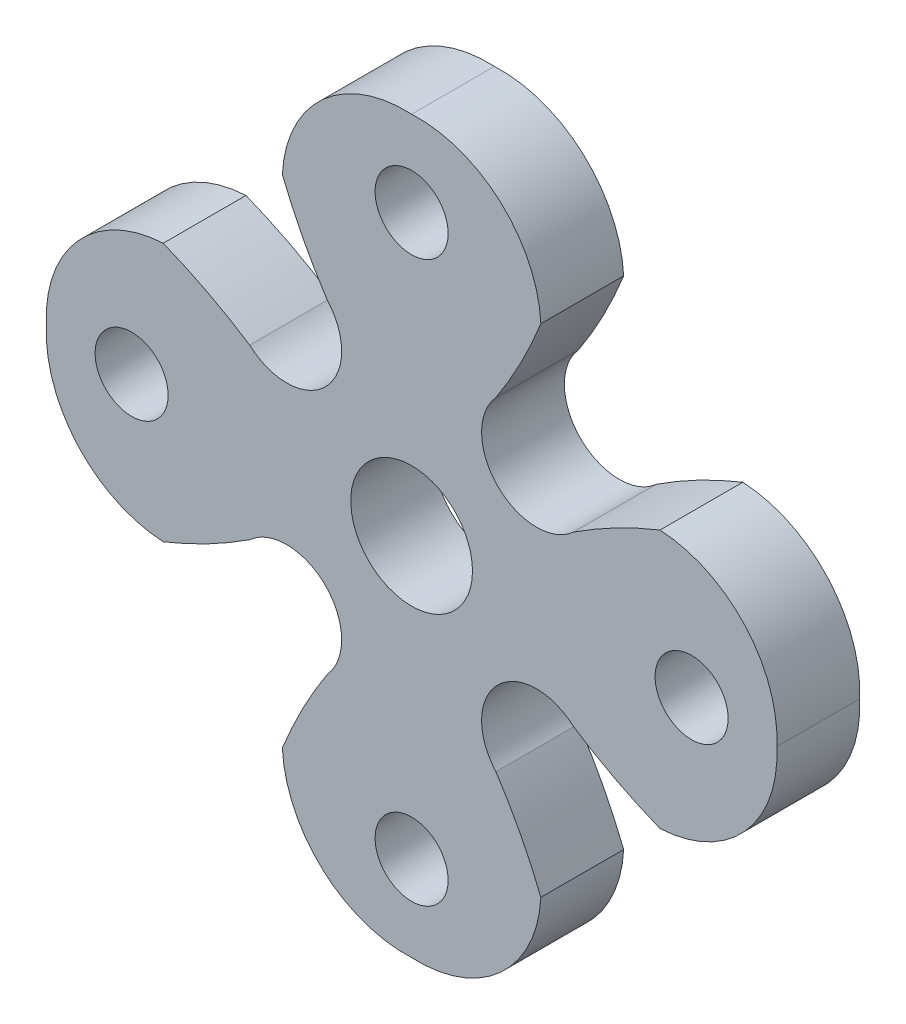
SolidWorks part; units mm, degrees
ref_plane "Front Plane" through (0, 0, 0) normal (0, 0, 1) x (1, 0, 0)
ref_plane "Top Plane" through (0, 0, 0) normal (0, 1, 0) x (1, 0, 0)
ref_plane "Right Plane" through (0, 0, 0) normal (1, 0, 0) x (0, 0, -1)
sketch "Sketch1" plane through (0, 0, 0) normal (0, 0, 1) x (1, 0, 0)
  line L0 (0, 0) -> (0, 19.05) construction
  line L1 (0, 0) -> (-35355.3391, -35355.3391) construction
  line L2 (0, 0) -> (-35355.3391, 35355.3391) construction
  circle A0 centre (0, 0) radius 19.05 construction
  circle A1 centre (0, 14.605) radius 1.905
  circle A2 centre (14.605, 0) radius 1.905
  circle A3 centre (0, -14.605) radius 1.905
  circle A4 centre (-14.605, 0) radius 1.905
  circle A5 centre (0, 0) radius 3.175
  circle A6 centre (0, 0) radius 6.35 construction
  circle A7 centre (0, 14.605) radius 4.445 construction
  circle A8 centre (0, 0) radius 14.605 construction
  circle A9 centre (10.3273, 10.3273) radius 4.445 construction
  circle A10 centre (10.3273, -10.3273) radius 4.445 construction
  circle A11 centre (-10.3273, -10.3273) radius 4.445 construction
  circle A12 centre (-10.3273, 10.3273) radius 4.445 construction
  arc A13 (-6.7425, 12.9555) -> (0, 19.05) centre (-0.324, 12.6315) cw
  arc A14 (6.7425, 12.9555) -> (0, 19.05) centre (0.324, 12.6315) ccw
  arc A15 (12.9555, 6.7425) -> (19.05, 0) centre (12.6315, 0.324) cw
  arc A16 (12.9555, -6.7425) -> (19.05, 0) centre (12.6315, -0.324) ccw
  arc A17 (6.7425, -12.9555) -> (0, -19.05) centre (0.324, -12.6315) cw
  arc A18 (-6.7425, -12.9555) -> (0, -19.05) centre (-0.324, -12.6315) ccw
  arc A19 (-12.9555, -6.7425) -> (-19.05, 0) centre (-12.6315, -0.324) cw
  arc A20 (-12.9555, 6.7425) -> (-19.05, 0) centre (-12.6315, 0.324) ccw
  circle A21 centre (0, 0) radius 9.525 construction
  arc A22 (-6.7425, 12.9555) -> (-4.3973, 8.4492) centre (16.8484, 22.3697) ccw
  arc A23 (6.7425, 12.9555) -> (4.3973, 8.4492) centre (-16.8484, 22.3697) cw
  arc A24 (12.9555, -6.7425) -> (8.4492, -4.3973) centre (22.3697, 16.8484) cw
  arc A25 (12.9555, 6.7425) -> (8.4492, 4.3973) centre (22.3697, -16.8484) ccw
  arc A26 (-6.7425, -12.9555) -> (-4.3973, -8.4492) centre (16.8484, -22.3697) cw
  arc A27 (6.7425, -12.9555) -> (4.3973, -8.4492) centre (-16.8484, -22.3697) ccw
  arc A28 (-12.9555, 6.7425) -> (-8.4492, 4.3973) centre (-22.3697, -16.8484) cw
  arc A29 (-12.9555, -6.7425) -> (-8.4492, -4.3973) centre (-22.3697, 16.8484) ccw
  arc A30 (-8.4492, 4.3973) -> (-4.3973, 8.4492) centre (-6.5183, 6.5183) ccw
  arc A31 (4.3973, 8.4492) -> (8.4492, 4.3973) centre (6.5183, 6.5183) ccw
  arc A32 (8.4492, -4.3973) -> (4.3973, -8.4492) centre (6.5183, -6.5183) ccw
  arc A33 (-4.3973, -8.4492) -> (-8.4492, -4.3973) centre (-6.5183, -6.5183) ccw
  point P15 (0, 0)
  point P32 (0, 0)
  point P52 (0, 0)
  point P76 (0, 0)
  point P81 (0, 0)
  dimension "D1" = 4.445
  dimension "D2" = 38.1
  dimension "D3" = 4
  dimension "D4" = 12.7
  dimension "D5" = 4
  dimension "D6" = 4
  dimension "D7" = 4
  dimension "D8" = 4
  dimension "D9" = 14.605
  dimension "D10" = 6.35
extrude "Boss-Extrude1" add sketch "Sketch1" along normal blind 4.318
